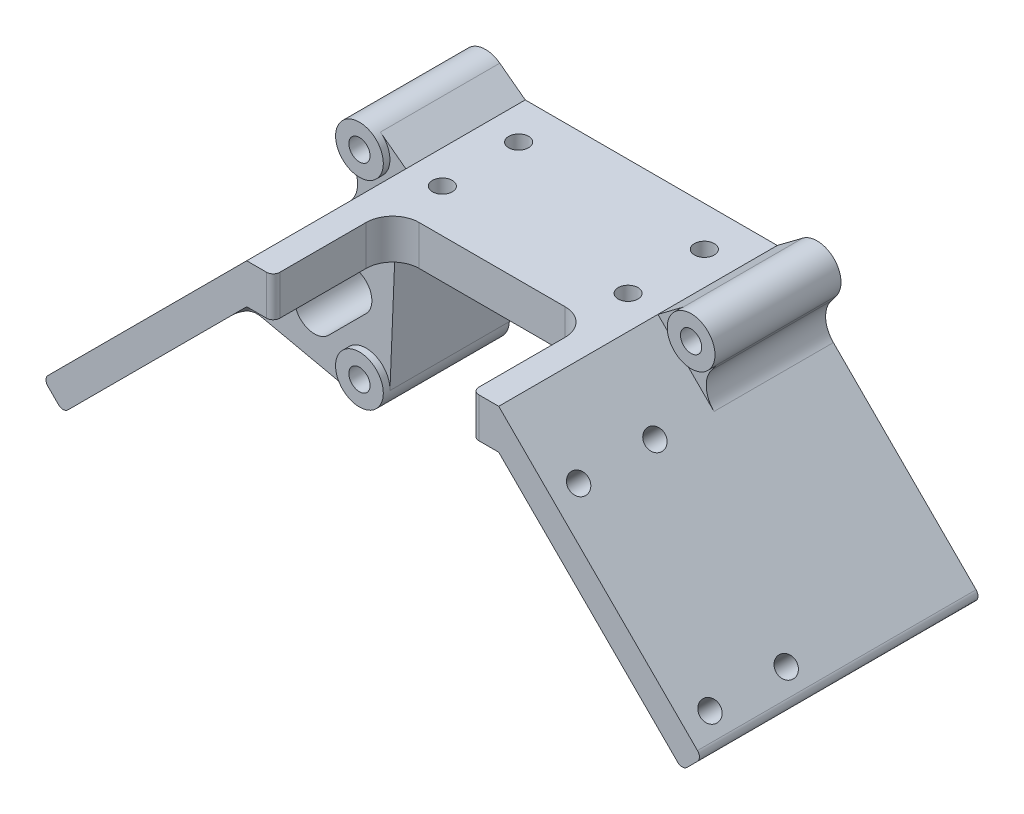
SolidWorks part; units mm, degrees
ref_plane "Plan de face" through (0, 0, 0) normal (0, 0, 1) x (1, 0, 0)
ref_plane "Plan de dessus" through (0, 0, 0) normal (0, 1, 0) x (1, 0, 0)
ref_plane "Plan de droite" through (0, 0, 0) normal (1, 0, 0) x (0, 0, -1)
sketch "Esquisse1" plane through (0, 0, 0) normal (0, 0, 1) x (1, 0, 0)
  line L1 (25, 15) -> (-25, 15) construction
  line L2 (25, 15) -> (25, -15) construction
  line L3 (25, -15) -> (-25, -15) construction
  line L4 (-25, 15) -> (-25, -15) construction
  line L5 (25, 15) -> (-25, -15) construction
  line L6 (25, -15) -> (-25, 15) construction
  line L7 (29, 19) -> (-29, 19)
  line L8 (29, 19) -> (29, -19)
  line L9 (29, -19) -> (-29, -19)
  line L10 (-29, 19) -> (-29, -19)
  line L11 (29, 19) -> (-29, -19) construction
  line L12 (29, -19) -> (-29, 19) construction
  circle A0 centre (-25, 15) radius 1.6
  circle A1 centre (-25, -15) radius 1.6
  circle A2 centre (25, 15) radius 1.6
  circle A3 centre (25, -15) radius 1.6
  point P0 (0, 0)
  point P10 (0, 0)
  dimension "D3" = 3.2
  dimension "D4" = 3.2
  dimension "D5" = 3.2
  dimension "D6" = 3.2
  dimension "D1" = 30
  dimension "D2" = 50
  dimension "D7" = 4
  dimension "D8" = 4
extrude "Boss.-Extru.1" add sketch "Esquisse1" along normal blind 2
sketch "Esquisse2" plane through (0, 0, 2) normal (0, 0, 1) x (1, 0, 0)
  line L0 (-29, -1) -> (-19, 9)
  line L1 (-29, 19) -> (-29, -19) construction
  line L2 (-19, 9) -> (19, 9)
  line L3 (0, 0) -> (0, 19) construction
  line L4 (29, 19) -> (-29, 19) construction
  line L5 (29, -1) -> (19, 9)
  line L6 (-29, -1) -> (-29, 5)
  line L7 (-29, 5) -> (-19, 15)
  line L8 (-19, 15) -> (0, 15)
  line L9 (0, 15) -> (19, 15)
  line L10 (19, 15) -> (29, 5)
  line L11 (29, -19) -> (29, 19) construction
  line L12 (29, 5) -> (29, -1)
  line L13 (-19, 9) -> (-19, 15) construction
  line L14 (19, 15) -> (19, 9) construction
  point P13 (0, 9)
  dimension "D1" = 38
  dimension "D2" = 45
  dimension "D3" = 4
  dimension "D4" = 6
extrude "Boss.-Extru.2" add sketch "Esquisse2" along normal blind 20
sketch "Esquisse3" plane through (0, 0, 22) normal (0, 0, 1) x (1, 0, 0)
  line L0 (-19, 15) -> (-49.6726, -15.6726)
  line L1 (-49.6726, -15.6726) -> (-46.6726, -18.6726)
  line L2 (-46.6726, -18.6726) -> (-19, 9)
  line L3 (-19, 9) -> (19, 9) construction
  line L4 (29, 19) -> (-29, 19) construction
  line L5 (-29, -1) -> (-19, 9) construction
  line L7 (0, 0) -> (0, 19) construction
  line L10 (46.6726, -18.6726) -> (19, 9)
  line L11 (49.6726, -15.6726) -> (46.6726, -18.6726)
  line L12 (19, 15) -> (49.6726, -15.6726)
  line L13 (-19, 15) -> (19, 15)
  line L14 (-19, 9) -> (19, 9)
  point P9 (0, 19)
extrude "Boss.-Extru.3" add sketch "Esquisse3" along normal blind 20
sketch "Esquisse4" plane through (0, 0, 2) normal (0, 0, 1) x (1, 0, 0)
  line L0 (-15, 5) -> (15, 5) construction
  line L1 (-15, 9) -> (15, 9)
  line L2 (-15, 1) -> (15, 1)
  line L3 (-19, 9) -> (19, 9) construction
  line L4 (0, -19) -> (0, 19) construction
  line L5 (-29, -19) -> (29, -19) construction
  line L6 (29, 19) -> (-29, 19) construction
  arc A0 (-15, 9) -> (-15, 1) centre (-15, 5) ccw
  arc A1 (15, 1) -> (15, 9) centre (15, 5) ccw
  point P2 (0, 5)
  point P15 (0, 5)
  point P16 (0, 5)
  dimension "D1" = 4
  dimension "D2" = 8
  dimension "D3" = 30
extrude "Enlèv. mat.-Extru.1" cut sketch "Esquisse4" against normal blind 20
sketch "Esquisse6" plane through (-14, 14, 0) normal (0.7071, -0.7071, 0) x (0, 0, -1)
  line L0 (-42, -46.206) -> (-22, -46.206) construction
  line L1 (-38, -42.206) -> (-26.5, -42.206) construction
  line L2 (-38, -42.206) -> (-38, -14.206) construction
  line L3 (-38, -14.206) -> (-26.5, -14.206) construction
  line L4 (-26.5, -42.206) -> (-26.5, -14.206) construction
  line L5 (-38, -42.206) -> (-26.5, -14.206) construction
  line L6 (-38, -14.206) -> (-26.5, -42.206) construction
  line L7 (-42, -46.206) -> (-42, -7.0711) construction
  circle A0 centre (-38, -42.206) radius 1.5
  circle A1 centre (-26.5, -14.206) radius 1.5
  circle A2 centre (-38, -14.206) radius 1.5
  circle A3 centre (-26.5, -42.206) radius 1.5
  point P4 (-32.25, -28.206)
  dimension "D1" = 3
  dimension "D2" = 3
  dimension "D7" = 3
  dimension "D8" = 3
  dimension "D3" = 11.5
  dimension "D4" = 28
  dimension "D5" = 4
  dimension "D6" = 4
extrude "Enlèv. mat.-Extru.2" cut sketch "Esquisse6" against normal blind 20
sketch "Esquisse7" plane through (14, 14, 0) normal (-0.7071, -0.7071, 0) x (0, 0, 1)
  line L0 (42, -7.0711) -> (42, -46.206) construction
  line L1 (38, -42.206) -> (26.5, -42.206) construction
  line L2 (38, -42.206) -> (38, -14.206) construction
  line L3 (38, -14.206) -> (26.5, -14.206) construction
  line L4 (26.5, -42.206) -> (26.5, -14.206) construction
  line L5 (38, -42.206) -> (26.5, -14.206) construction
  line L6 (38, -14.206) -> (26.5, -42.206) construction
  line L7 (42, -46.206) -> (22, -46.206) construction
  circle A0 centre (38, -14.206) radius 1.5
  circle A1 centre (38, -42.206) radius 1.5
  circle A2 centre (26.5, -42.206) radius 1.5
  circle A3 centre (26.5, -14.206) radius 1.5
  point P0 (32.25, -28.206)
  point P11 (23.5, -15.0666)
  dimension "D5" = 3
  dimension "D6" = 3
  dimension "D7" = 3
  dimension "D8" = 3
  dimension "D1" = 11.5
  dimension "D2" = 28
  dimension "D3" = 4
  dimension "D4" = 4
extrude "Enlèv. mat.-Extru.3" cut sketch "Esquisse7" against normal blind 20
sketch "Esquisse8" plane through (0, 9, 0) normal (0, -1, 0) x (1, 0, 0)
  line L0 (0, 0) -> (0, 42) construction
  line L1 (14, 17.5) -> (-14, 17.5) construction
  line L2 (14, 17.5) -> (14, 6) construction
  line L3 (14, 6) -> (-14, 6) construction
  line L4 (-14, 17.5) -> (-14, 6) construction
  line L5 (14, 17.5) -> (-14, 6) construction
  line L6 (14, 6) -> (-14, 17.5) construction
  line L7 (-19, 42) -> (19, 42) construction
  line L10 (-29, 2) -> (29, 2) construction
  circle A0 centre (-14, 17.5) radius 1.5
  circle A1 centre (14, 17.5) radius 1.5
  circle A2 centre (14, 6) radius 1.5
  circle A3 centre (-14, 6) radius 1.5
  point P0 (0, 11.75)
  dimension "D4" = 3
  dimension "D5" = 3
  dimension "D6" = 3
  dimension "D7" = 3
  dimension "D1" = 11.5
  dimension "D2" = 28
  dimension "D3" = 4
extrude "Enlèv. mat.-Extru.4" cut sketch "Esquisse8" against normal blind 20
sketch "Esquisse9" plane through (0, 0, 22) normal (0, 0, -1) x (-1, 0, 0)
  line L4 (49.6726, -15.6726) -> (29, 5)
  line L5 (29, 5) -> (29, -1)
  line L6 (29, -1) -> (46.6726, -18.6726)
  line L7 (46.6726, -18.6726) -> (49.6726, -15.6726)
  line L8 (49.6726, -15.6726) -> (29, 5)
  line L9 (29, 5) -> (29, -1)
  line L10 (29, -1) -> (46.6726, -18.6726)
  line L11 (46.6726, -18.6726) -> (49.6726, -15.6726)
  line L12 (-46.6726, -18.6726) -> (-29, -1)
  line L13 (-29, -1) -> (-29, 5)
  line L14 (-29, 5) -> (-49.6726, -15.6726)
  line L15 (-49.6726, -15.6726) -> (-46.6726, -18.6726)
  line L16 (-46.6726, -18.6726) -> (-29, -1)
  line L17 (-29, -1) -> (-29, 5)
  line L18 (-29, 5) -> (-49.6726, -15.6726)
  line L19 (-49.6726, -15.6726) -> (-46.6726, -18.6726)
  dimension "D1" = 0
  dimension "D2" = 0
extrude "Boss.-Extru.5" add sketch "Esquisse9" along normal blind 22
sketch "Esquisse10" plane through (0, 9, 0) normal (0, -1, 0) x (1, 0, 0)
  line L0 (-19, 42) -> (19, 42) construction
  line L1 (-15, 42) -> (15, 42)
  line L2 (-15, 42) -> (-15, 24)
  line L3 (-15, 24) -> (15, 24)
  line L4 (15, 42) -> (15, 24)
  line L5 (-15, 42) -> (15, 24) construction
  line L6 (-15, 24) -> (15, 42) construction
  line L7 (-19, 42) -> (-19, 2) construction
  line L8 (19, 42) -> (19, 2) construction
  line L9 (-29, 0) -> (29, 0) construction
  point P4 (0, 33)
  dimension "D1" = 4
  dimension "D2" = 4
  dimension "D3" = 24
extrude "Enlèv. mat.-Extru.5" cut sketch "Esquisse10" against normal blind 20
sketch "Esquisse11" plane through (0, 0, 2) normal (0, 0, 1) x (1, 0, 0)
  circle A0 centre (-25, -15) radius 1.6 construction
  circle A1 centre (25, -15) radius 1.6 construction
  circle A2 centre (25, 15) radius 1.6 construction
  circle A3 centre (-25, 15) radius 1.6 construction
  circle A4 centre (-25, -15) radius 1.6
  circle A5 centre (25, -15) radius 1.6
  circle A6 centre (25, 15) radius 1.6
  circle A7 centre (-25, 15) radius 1.6
  circle A8 centre (-25, -15) radius 3.6
  circle A9 centre (25, -15) radius 3.6
  circle A10 centre (25, 15) radius 3.6
  circle A11 centre (-25, 15) radius 3.6
  dimension "D1" = 2
extrude "Boss.-Extru.6" add sketch "Esquisse11" along normal blind 17
sketch "Esquisse12" plane through (0, 0, 0) normal (0, 0, -1) x (-1, 0, 0)
  line L0 (46.6726, -18.6726) -> (29, -19)
  line L1 (29, -19) -> (29, -1)
  line L2 (29, -1) -> (46.6726, -18.6726) construction
  line L3 (29, -1) -> (46.6726, -18.6726)
  line L4 (-29, -19) -> (-46.6726, -18.6726)
  line L5 (-46.6726, -18.6726) -> (-29, -1)
  line L6 (-29, -1) -> (-29, -19)
  line L7 (29, 19) -> (49.6726, -15.6726)
  line L8 (49.6726, -15.6726) -> (29, 5)
  line L9 (29, 5) -> (29, 19)
  line L10 (-29, 19) -> (-29, 5)
  line L11 (-29, 5) -> (-49.6726, -15.6726)
  line L12 (-49.6726, -15.6726) -> (-29, 19)
  line L13 (-29, -19) -> (-29, -1) construction
  line L14 (46.6726, -18.6726) -> (49.6726, -15.6726) construction
  point P23 (-29, -1)
  point P26 (-29, -1)
  point P29 (0, 0)
  point P30 (-29, 5)
  point P31 (0, 0)
  point P32 (-49.6726, -15.6726)
  point P34 (0, 0)
  point P35 (-46.6726, -18.6726)
  point P37 (0, 0)
  point P38 (29, 5)
  point P40 (0, 0)
  point P41 (49.6726, -15.6726)
  point P44 (0, 0)
  point P45 (46.6726, -18.6726)
extrude "Boss.-Extru.7" add sketch "Esquisse12" against normal blind 2
sketch "Esquisse13" plane through (0, 0, 2) normal (0, 0, 1) x (1, 0, 0)
  line L0 (-25, -15) -> (-32.8363, -4.8363) construction
  line L1 (-46.6726, -18.6726) -> (-19, 9) construction
  line L2 (0, 19) -> (0, -19) construction
  line L3 (29, 19) -> (-29, 19) construction
  line L4 (-29, -19) -> (29, -19) construction
  line L5 (-22.84, 17.88) -> (-19, 15)
  line L6 (-27.88, 12.84) -> (-25, 9)
  line L7 (-19, 15) -> (-49.6726, -15.6726) construction
  line L8 (-25, 15) -> (-22, 12) construction
  line L9 (-25, 9) -> (-19, 15)
  line L10 (25, 15) -> (22, 12) construction
  line L11 (25, 9) -> (19, 15)
  line L12 (27.88, 12.84) -> (25, 9)
  line L13 (22.84, 17.88) -> (19, 15)
  line L14 (-21.4031, -15.1487) -> (-20.4652, 7.5348)
  line L15 (-46.6726, -18.6726) -> (-19, 9) construction
  line L16 (-25.7711, -18.5165) -> (-42.7856, -14.7856)
  line L17 (-42.7856, -14.7856) -> (-20.4652, 7.5348)
  line L18 (-42.7856, -14.7856) -> (-20.4652, 7.5348)
  line L19 (25, -15) -> (32.8363, -4.8363) construction
  line L20 (42.7856, -14.7856) -> (20.4652, 7.5348)
  line L21 (42.7856, -14.7856) -> (20.4652, 7.5348)
  line L22 (25.7711, -18.5165) -> (42.7856, -14.7856)
  line L23 (21.4031, -15.1487) -> (20.4652, 7.5348)
  circle A0 centre (-25, 15) radius 3.6 construction
  arc A1 (-27.88, 12.84) -> (-22.84, 17.88) centre (-25, 15) cw
  circle A2 centre (-25, 15) radius 1.6 construction
  circle A3 centre (-25, 15) radius 1.6
  circle A4 centre (25, 15) radius 1.6
  arc A5 (27.88, 12.84) -> (22.84, 17.88) centre (25, 15) ccw
  circle A6 centre (-25, -15) radius 3.6 construction
  circle A7 centre (-25, -15) radius 3.6 construction
  arc A8 (-21.4031, -15.1487) -> (-25.7711, -18.5165) centre (-25, -15) cw
  circle A9 centre (-25, -15) radius 1.6 construction
  circle A10 centre (-25, -15) radius 1.6
  circle A11 centre (25, -15) radius 1.6
  arc A12 (21.4031, -15.1487) -> (25.7711, -18.5165) centre (25, -15) ccw
  circle M7 centre (-25, -15) radius 3.6
  line M11 (-19, 9) -> (-46.6726, -18.6726)
  line M15 (46.6726, -18.6726) -> (19, 9)
  circle M18 centre (25, -15) radius 3.6
  dimension "D1" = 80
extrude "Boss.-Extru.8" add sketch "Esquisse13" along normal blind 16 contours A1 L6 L9 L5 A3 | L16 L14 M7 M11 | L23 L22 M18 M15 | L12 A5 L13 L11 A4
sketch "Esquisse14" plane through (0, 0, 2) normal (0, 0, 1) x (1, 0, 0)
  line L10 (27.88, 12.84) -> (25, 9)
  line L11 (25, 9) -> (49.6726, -15.6726)
  line L12 (49.6726, -15.6726) -> (29, 19)
  line L13 (29, 19) -> (-29, 19)
  line L14 (49.6726, -15.6726) -> (29, 19)
  line L15 (-49.6726, -15.6726) -> (-25, 9)
  line L16 (-25, 9) -> (-27.88, 12.84)
  line L17 (-22.84, 17.88) -> (-19, 15)
  line L18 (-19, 15) -> (19, 15)
  line L19 (19, 15) -> (22.84, 17.88)
  line L20 (27.88, 12.84) -> (25, 9)
  line L21 (25, 9) -> (49.6726, -15.6726)
  line L22 (-29, 19) -> (-49.6726, -15.6726)
  line L23 (29, 19) -> (-29, 19)
  line L24 (-29, 19) -> (-49.6726, -15.6726)
  line L25 (-49.6726, -15.6726) -> (-25, 9)
  line L26 (-25, 9) -> (-27.88, 12.84)
  line L27 (-22.84, 17.88) -> (-19, 15)
  line L28 (-19, 15) -> (19, 15)
  line L29 (19, 15) -> (22.84, 17.88)
  line L32 (-42.7856, -14.7856) -> (-46.6726, -18.6726)
  line L33 (-42.7856, -14.7856) -> (-46.6726, -18.6726)
  line L34 (21.4031, -15.1487) -> (20.4652, 7.5348)
  line L35 (20.4652, 7.5348) -> (19, 9)
  line L36 (19, 9) -> (15, 9)
  line L37 (15, 1) -> (-15, 1)
  line L38 (-15, 9) -> (-19, 9)
  line L39 (-19, 9) -> (-20.4652, 7.5348)
  line L40 (-20.4652, 7.5348) -> (-21.4031, -15.1487)
  line L41 (-25.7711, -18.5165) -> (-42.7856, -14.7856)
  line L42 (-46.6726, -18.6726) -> (-29, -19)
  line L43 (-46.6726, -18.6726) -> (-29, -19)
  line L44 (-29, -19) -> (29, -19)
  line L47 (42.7856, -14.7856) -> (25.7711, -18.5165)
  line L48 (21.4031, -15.1487) -> (20.4652, 7.5348)
  line L49 (20.4652, 7.5348) -> (19, 9)
  line L50 (19, 9) -> (15, 9)
  line L51 (15, 1) -> (-15, 1)
  line L52 (-15, 9) -> (-19, 9)
  line L53 (-19, 9) -> (-20.4652, 7.5348)
  line L54 (-20.4652, 7.5348) -> (-21.4031, -15.1487)
  line L55 (-25.7711, -18.5165) -> (-42.7856, -14.7856)
  line L56 (29, -19) -> (46.6726, -18.6726)
  line L57 (29, -19) -> (46.6726, -18.6726)
  line L58 (-29, -19) -> (29, -19)
  line L59 (46.6726, -18.6726) -> (42.7856, -14.7856)
  line L60 (46.6726, -18.6726) -> (42.7856, -14.7856)
  line L61 (42.7856, -14.7856) -> (25.7711, -18.5165)
  arc A2 (27.88, 12.84) -> (22.84, 17.88) centre (25, 15) ccw
  arc A3 (-22.84, 17.88) -> (-27.88, 12.84) centre (-25, 15) ccw
  arc A4 (27.88, 12.84) -> (22.84, 17.88) centre (25, 15) ccw
  arc A5 (-22.84, 17.88) -> (-27.88, 12.84) centre (-25, 15) ccw
  arc A8 (21.4031, -15.1487) -> (25.7711, -18.5165) centre (25, -15) ccw
  arc A9 (15, 1) -> (15, 9) centre (15, 5) ccw
  arc A10 (-15, 9) -> (-15, 1) centre (-15, 5) ccw
  arc A11 (-25.7711, -18.5165) -> (-21.4031, -15.1487) centre (-25, -15) ccw
  arc A12 (21.4031, -15.1487) -> (25.7711, -18.5165) centre (25, -15) ccw
  arc A13 (15, 1) -> (15, 9) centre (15, 5) ccw
  arc A14 (-15, 9) -> (-15, 1) centre (-15, 5) ccw
  arc A15 (-25.7711, -18.5165) -> (-21.4031, -15.1487) centre (-25, -15) ccw
  dimension "D1" = 0
  dimension "D2" = 0
extrude "Enlèv. mat.-Extru.6" cut sketch "Esquisse14" against normal blind 16
fillet "Congé1" radius 4 8 edges at (-25, 9, 9) (25, 9, 9) (42.7856, -14.7856, 9) (20.4652, 7.5348, 9) (-20.4652, 7.5348, 9) (-42.7856, -14.7856, 9) (15, 12, 24) (-15, 12, 24)
fillet "Congé2" radius 1 4 edges at (-46.6726, -18.6726, 21) (-49.6726, -15.6726, 21) (46.6726, -18.6726, 21) (49.6726, -15.6726, 21)
fillet "Congé3" radius 1 2 edges at (-15, 12, 42) (15, 12, 42)
fillet "Congé4" radius 1 2 edges at (31.8473, -3.8473, 18) (-31.8473, -3.8473, 18)
sketch "Esquisse15" plane through (0, 0, 18) normal (0, 0, 1) x (1, 0, 0)
  line L0 (-32.7816, -10.4384) -> (-27.1247, -4.7816) construction
  line L1 (-34.9029, -8.3171) -> (-29.246, -2.6602)
  line L2 (-30.6602, -12.5597) -> (-25.0034, -6.9029)
  line L3 (-20.5252, 6.0605) -> (-41.7552, -15.1694) construction
  line L4 (0, 0) -> (0, 15) construction
  line L5 (-11, 15) -> (11, 15) construction
  line L6 (32.7816, -10.4384) -> (27.1247, -4.7816) construction
  line L7 (34.9029, -8.3171) -> (29.246, -2.6602)
  line L8 (30.6602, -12.5597) -> (25.0034, -6.9029)
  arc A0 (-34.9029, -8.3171) -> (-30.6602, -12.5597) centre (-32.7816, -10.4384) ccw
  arc A1 (-25.0034, -6.9029) -> (-29.246, -2.6602) centre (-27.1247, -4.7816) ccw
  arc A2 (34.9029, -8.3171) -> (30.6602, -12.5597) centre (32.7816, -10.4384) cw
  arc A3 (25.0034, -6.9029) -> (29.246, -2.6602) centre (27.1247, -4.7816) cw
  point P2 (-29.9531, -7.61)
  point P16 (29.9531, -7.61)
  dimension "D1" = 8
  dimension "D2" = 6
extrude "Enlèv. mat.-Extru.7" cut sketch "Esquisse15" against normal through all
